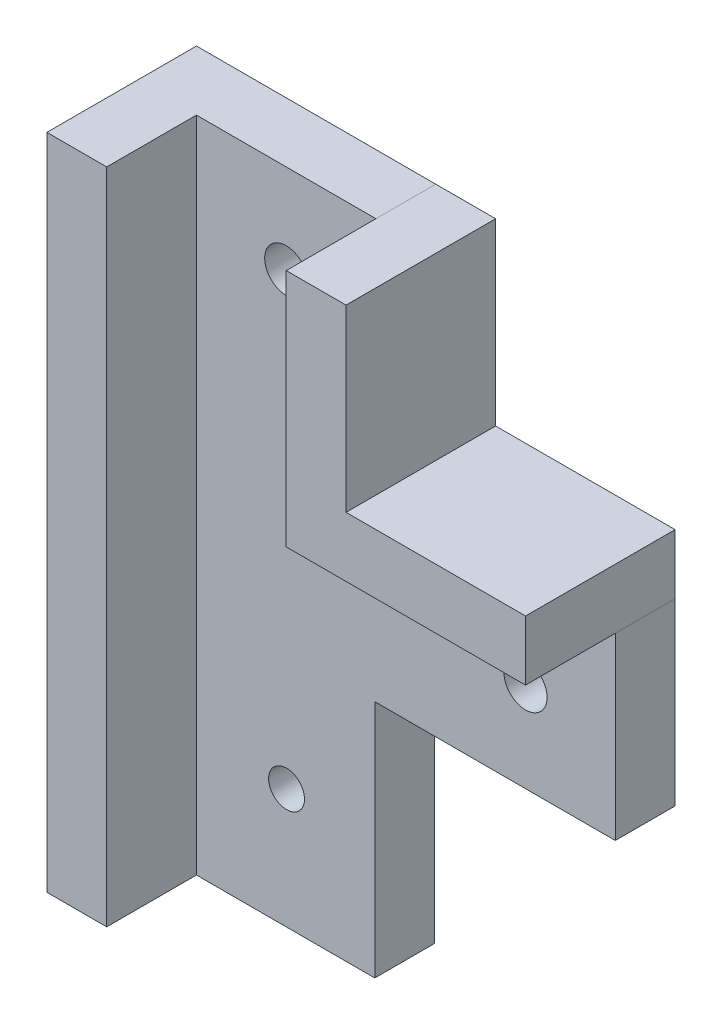
SolidWorks part; units mm, degrees
ref_plane "前视基准面" through (0, 0, 0) normal (0, 0, 1) x (1, 0, 0)
ref_plane "上视基准面" through (0, 0, 0) normal (0, 1, 0) x (1, 0, 0)
ref_plane "右视基准面" through (0, 0, 0) normal (1, 0, 0) x (0, 0, -1)
sketch "Sketch1" plane through (0, 0, 0) normal (0, 0, 1) x (1, 0, 0)
  line L0 (7.3701, -25.8068) -> (27.4701, -25.8068)
  line L3 (-7.5299, 9.1932) -> (7.4701, 9.1932)
  line L4 (-7.5299, 9.1932) -> (-7.5299, -25.8068)
  line L6 (7.4701, 9.1932) -> (7.4701, -10.8068)
  line L7 (27.4701, -25.8068) -> (27.4701, -10.8068)
  line L8 (27.4701, -10.8068) -> (7.4701, -10.8068)
  line L12 (-7.5299, -25.8068) -> (7.3701, -25.8068)
  dimension "D1" = 15
  dimension "D2" = 35
  dimension "D3" = 35
  dimension "D4" = 15
extrude "Boss-Extrude1" add sketch "Sketch1" along normal blind 5
sketch "Sketch2" plane through (0, 0, 0) normal (0, 0, -1) x (-1, 0, 0)
  line L0 (-7.4701, 9.1932) -> (-12.4701, 9.1932)
  line L1 (-12.4701, 9.1932) -> (-12.4701, -5.8068)
  line L2 (-12.4701, -5.8068) -> (-27.4701, -5.8068)
  line L3 (-27.4701, -10.8068) -> (-27.4701, -5.8068)
  line L4 (-27.4701, -10.8068) -> (-7.4701, -10.8068)
  line L5 (-7.4701, -10.8068) -> (-7.4701, 9.1932)
  dimension "D1" = 5
  dimension "D2" = 5
extrude "Boss-Extrude2" add sketch "Sketch2" against normal blind 12.5 separate body
sketch "Sketch3" plane through (0, 0, 0) normal (0, 0, -1) x (-1, 0, 0)
  line L0 (7.5299, 9.1932) -> (12.5299, 9.1932)
  line L2 (12.5299, -45.8068) -> (12.5299, 9.1932)
  line L3 (7.5299, -25.8068) -> (7.5299, 9.1932)
  line L5 (7.5299, -25.8068) -> (7.5299, -45.8068)
  line L6 (7.5299, -45.8068) -> (12.5299, -45.8068)
  dimension "D1" = 5
  dimension "D2" = 55
extrude "Boss-Extrude3" add sketch "Sketch3" against normal blind 12.5 separate body
sketch "Sketch4" plane through (0, 0, 0) normal (0, 0, -1) x (-1, 0, 0)
  line L0 (-27.4701, -10.8068) -> (-7.4701, -10.8068) construction
  line L1 (-27.4701, -25.8068) -> (-27.4701, -10.8068) construction
  line L2 (-7.4701, -10.8068) -> (-7.4701, 9.1932) construction
  line L3 (-7.4701, 9.1932) -> (7.5299, 9.1932) construction
  circle A0 centre (0.0299, 1.6932) radius 1.8
  circle A1 centre (-19.9701, -18.3068) radius 1.8
  dimension "D1" = 3.6
  dimension "D2" = 3.6
  dimension "D3" = 7.5
  dimension "D4" = 7.5
  dimension "D5" = 7.5
  dimension "D6" = 7.5
extrude "Cut-Extrude1" cut sketch "Sketch4" against normal through all
sketch "Sketch6" plane through (0, 0, 5) normal (0, 0, 1) x (1, 0, 0)
  line L0 (-7.5299, -25.8068) -> (-7.5299, -45.8068)
  line L1 (-7.5299, -25.8068) -> (27.4701, -25.8068) construction
  line L2 (-7.5299, -45.8068) -> (7.3701, -45.8068)
  line L3 (7.3701, -45.8068) -> (7.3701, -25.8068)
  line L4 (7.3701, -25.8068) -> (-7.5299, -25.8068)
  dimension "D1" = 14.9
  dimension "D2" = 20
extrude "Boss-Extrude4" add sketch "Sketch6" against normal blind 5
sketch "Sketch8" plane through (0, 0, 5) normal (0, 0, 1) x (1, 0, 0)
  line L0 (-7.5299, -45.8068) -> (7.3701, -45.8068) construction
  circle A0 centre (0, -35.8068) radius 1.5
  dimension "D1" = 3
  dimension "D2" = 10
extrude "Cut-Extrude2" cut sketch "Sketch8" against normal through all
